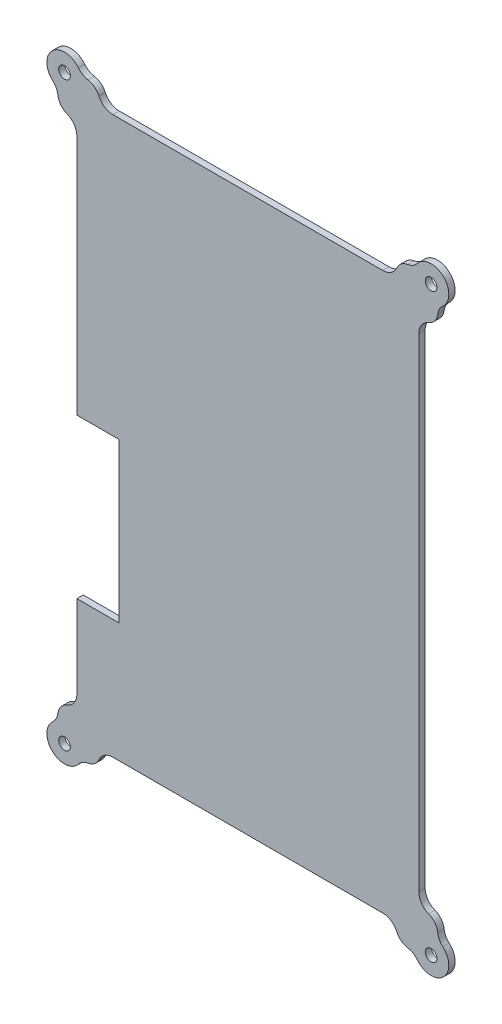
SolidWorks part; units mm, degrees
ref_plane "Front Plane" through (0, 0, 0) normal (0, 0, 1) x (1, 0, 0)
ref_plane "Top Plane" through (0, 0, 0) normal (0, 1, 0) x (1, 0, 0)
ref_plane "Right Plane" through (0, 0, 0) normal (1, 0, 0) x (0, 0, -1)
sketch "Sketch2" plane through (0, 0, 0) normal (0, 0, 1) x (1, 0, 0)
  line L0 (27.7407, 131.5) -> (47.7407, 131.5)
  line L1 (47.7407, 131.5) -> (47.7407, 56.5)
  line L14 (189.1282, 17.4051) -> (189.1282, 245.5949)
  line L15 (172.1341, 262.83) -> (44.7348, 262.83)
  line L16 (27.7407, 245.5949) -> (27.7407, 17.4051)
  line L17 (44.7348, 0.17) -> (172.1341, 0.17)
  line L18 (47.7407, 56.5) -> (27.7407, 56.5)
  arc A85 (193.7355, 252.2912) -> (189.1282, 245.5949) centre (196.2982, 245.5949) ccw
  arc A86 (193.7355, 252.2912) -> (198.0769, 257.8665) centre (191.2943, 258.6701) ccw
  arc A87 (200.4593, 262.4045) -> (198.0769, 257.8665) centre (205.1971, 257.0228) ccw
  arc A88 (200.4593, 262.4045) -> (188.4049, 273.8031) centre (194.9551, 268.6569) ccw
  arc A89 (183.8943, 271.1519) -> (188.4049, 273.8031) centre (182.7668, 278.2327) ccw
  arc A90 (183.8943, 271.1519) -> (178.707, 267.1355) centre (184.9683, 264.4069) ccw
  arc A91 (172.1341, 262.83) -> (178.707, 267.1355) centre (172.1341, 270) ccw
  arc A92 (38.1619, 267.1355) -> (44.7348, 262.83) centre (44.7348, 270) ccw
  arc A93 (38.1619, 267.1355) -> (32.9746, 271.1519) centre (31.9006, 264.4069) ccw
  arc A94 (28.4641, 273.8031) -> (32.9746, 271.1519) centre (34.1021, 278.2327) ccw
  arc A95 (28.4641, 273.8031) -> (16.4096, 262.4045) centre (21.9139, 268.6569) ccw
  arc A96 (18.792, 257.8665) -> (16.4096, 262.4045) centre (11.6718, 257.0228) ccw
  arc A97 (18.792, 257.8665) -> (23.1334, 252.2912) centre (25.5746, 258.6701) ccw
  arc A98 (27.7407, 245.5949) -> (23.1334, 252.2912) centre (20.5707, 245.5949) ccw
  arc A99 (23.1334, 10.7088) -> (27.7407, 17.4051) centre (20.5707, 17.4051) ccw
  arc A100 (23.1334, 10.7088) -> (18.792, 5.1335) centre (25.5746, 4.3299) ccw
  arc A101 (16.4096, 0.5955) -> (18.792, 5.1335) centre (11.6718, 5.9772) ccw
  arc A102 (16.4096, 0.5955) -> (28.4641, -10.8031) centre (21.9139, -5.6569) ccw
  arc A103 (32.9746, -8.1519) -> (28.4641, -10.8031) centre (34.1021, -15.2327) ccw
  arc A104 (32.9746, -8.1519) -> (38.1619, -4.1355) centre (31.9006, -1.4069) ccw
  arc A105 (44.7348, 0.17) -> (38.1619, -4.1355) centre (44.7348, -7) ccw
  arc A106 (178.707, -4.1355) -> (172.1341, 0.17) centre (172.1341, -7) ccw
  arc A107 (178.707, -4.1355) -> (183.8943, -8.1519) centre (184.9683, -1.4069) ccw
  arc A108 (188.4049, -10.8031) -> (183.8943, -8.1519) centre (182.7668, -15.2327) ccw
  arc A109 (188.4049, -10.8031) -> (200.4593, 0.5955) centre (194.9551, -5.6569) ccw
  arc A110 (198.0769, 5.1335) -> (200.4593, 0.5955) centre (205.1971, 5.9772) ccw
  arc A111 (198.0769, 5.1335) -> (193.7355, 10.7088) centre (191.2943, 4.3299) ccw
  arc A112 (189.1282, 17.4051) -> (193.7355, 10.7088) centre (196.2982, 17.4051) ccw
  circle A117 centre (21.9139, -5.6569) radius 2.75
  circle A118 centre (194.9551, -5.6569) radius 2.75
  circle A119 centre (194.9551, 268.6569) radius 2.75
  circle A120 centre (21.9139, 268.6569) radius 2.75
extrude "Boss-Extrude2" add sketch "Sketch2" along normal blind 3 contours A112 L14 A85 A86 A87 A88 A89 A90 A91 L15 A92 A93 A94 A95 A96 A97 A98 L16 L0 L1 L18 A99 A100 A101 A102 A103 A104 A105 L17 A106 A107 A108 A109 A110 A111 A120 A119 A118 A117
